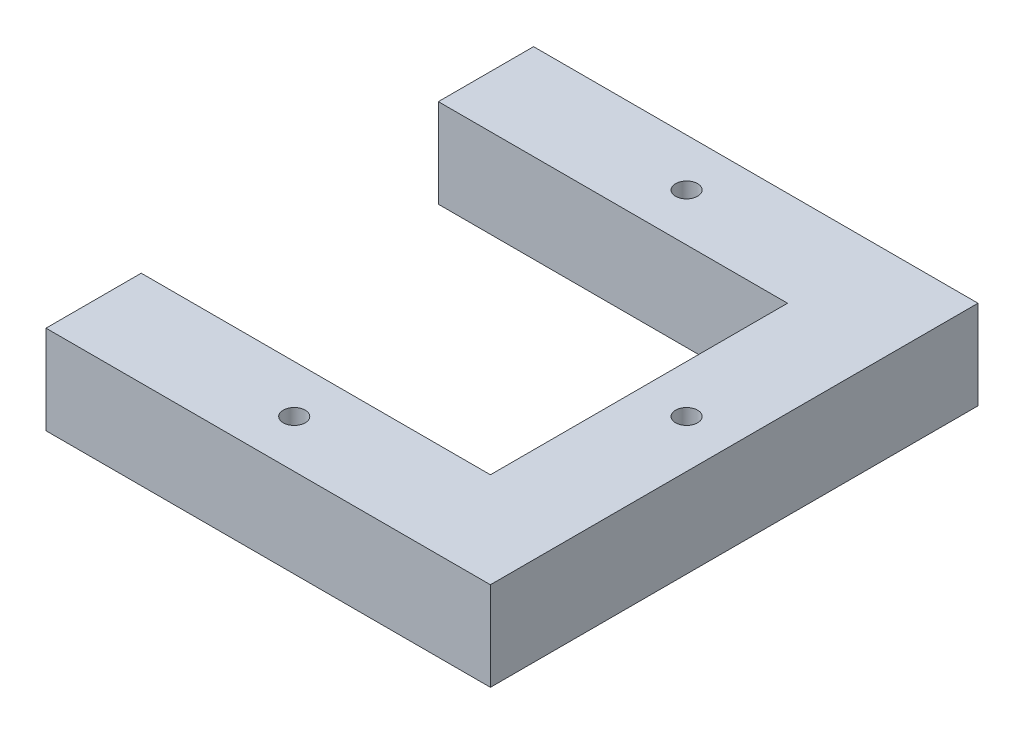
SolidWorks part; units mm, degrees
ref_plane "Front Plane" through (0, 0, 0) normal (0, 0, 1) x (1, 0, 0)
ref_plane "Top Plane" through (0, 0, 0) normal (0, 1, 0) x (1, 0, 0)
ref_plane "Right Plane" through (0, 0, 0) normal (1, 0, 0) x (0, 0, -1)
sketch "Sketch1" plane through (0, 0, 0) normal (0, 1, 0) x (1, 0, 0)
  line L0 (-80.2611, 59.4389) -> (-80.2611, 97.5389)
  line L1 (-80.2611, 97.5389) -> (97.5389, 97.5389)
  line L2 (97.5389, 97.5389) -> (97.5389, -97.5389)
  line L3 (97.5389, -97.5389) -> (-80.2611, -97.5389)
  line L4 (-80.2611, -97.5389) -> (-80.2611, -59.4389)
  line L5 (-80.2611, -59.4389) -> (59.4389, -59.4389)
  line L6 (59.4389, -59.4389) -> (59.4389, 59.4389)
  line L7 (-80.2611, 59.4389) -> (59.4389, 59.4389)
  line L8 (-80.2611, 78.4889) -> (78.4889, 78.4889) construction
  line L9 (-80.2611, -78.4889) -> (78.4889, -78.4889) construction
  line L10 (78.4889, -78.4889) -> (78.4889, 78.4889) construction
  circle A0 centre (0, 78.4889) radius 4.4
  circle A1 centre (0, -78.4889) radius 4.4
  circle A2 centre (78.4889, 0) radius 4.4
  point P10 (59.4389, 0)
  dimension "D8" = 8.8
  dimension "D9" = 177.8
  dimension "D5" = 78.4889
  dimension "D1" = 78.4889
  dimension "D2" = 38.1
  dimension "D3" = 38.1
  dimension "D4" = 19.05
  dimension "D6" = 19.05
  dimension "D7" = 177.8
extrude "Boss-Extrude1" add sketch "Sketch1" along normal blind 35.56
